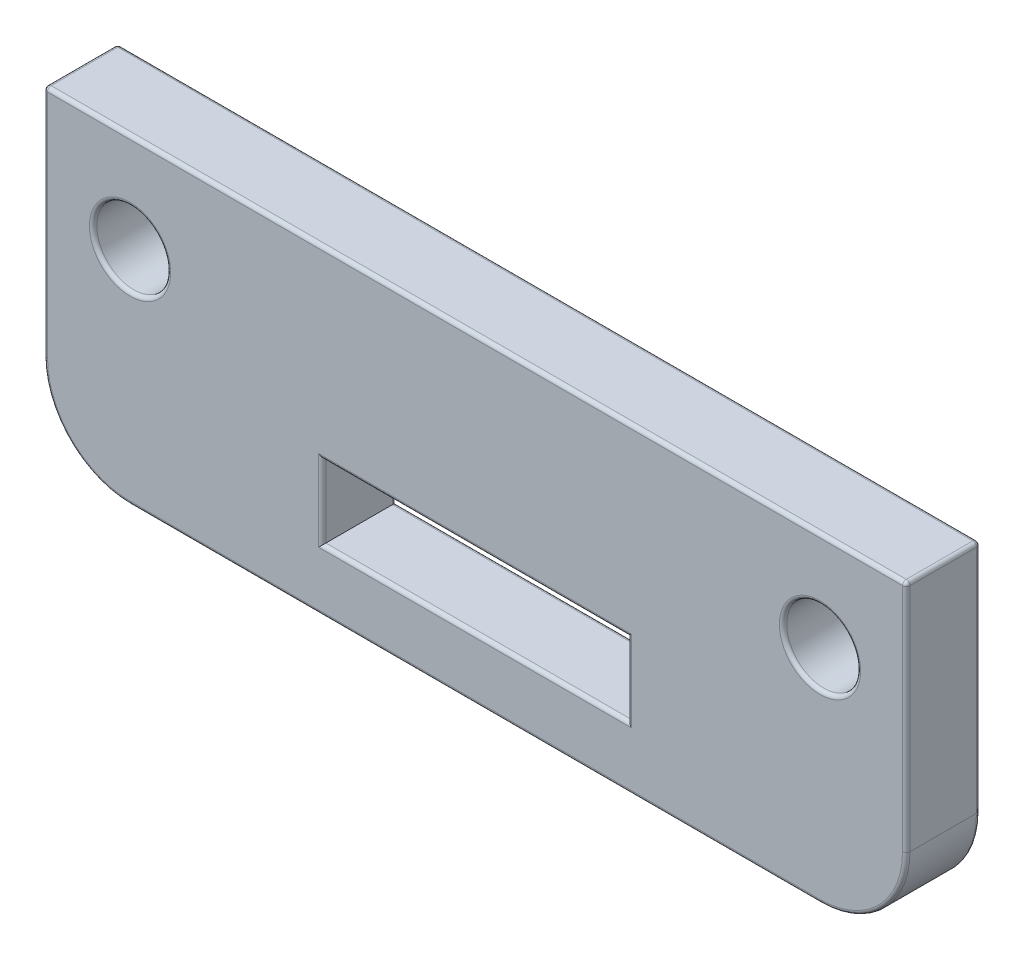
SolidWorks part; units mm, degrees
material "Balsa"
ref_plane "Front Plane" through (0, 0, 0) normal (0, 0, 1) x (1, 0, 0)
ref_plane "Top Plane" through (0, 0, 0) normal (0, 1, 0) x (1, 0, 0)
ref_plane "Right Plane" through (0, 0, 0) normal (1, 0, 0) x (0, 0, -1)
sketch "Sketch1" plane through (0, 0, 0) normal (0, 0, 1) x (1, 0, 0)
  line L0 (0, -19) -> (0, 26) construction
  line L1 (11.5, -6) -> (-11.5, -6)
  line L2 (11.5, -6) -> (11.5, 6)
  line L3 (11.5, 6) -> (-11.5, 6)
  line L4 (-11.5, -6) -> (-11.5, 6)
  line L5 (11.5, -6) -> (-11.5, 6) construction
  line L6 (11.5, 6) -> (-11.5, -6) construction
  line L7 (-6.2, -15) -> (6.2, -15) construction
  line L8 (-6.2, -13.5) -> (6.2, -13.5)
  line L9 (-6.2, -16.5) -> (6.2, -16.5)
  line L10 (-6.2, -13.5) -> (-6.2, -16.5)
  line L11 (-17.5, 9) -> (17.5, 9) construction
  line L12 (-17.5, 9) -> (-17.5, -19)
  line L13 (-17.5, -19) -> (17.5, -19)
  line L14 (17.5, 9) -> (17.5, -19)
  line L15 (6.2, -13.5) -> (6.2, -16.5)
  circle A0 centre (-14, 0) radius 1
  circle A1 centre (-14, -10) radius 1.5
  circle A4 centre (-8.5, 16) radius 2
  circle A5 centre (14, -10) radius 1.5
  circle A6 centre (14, 0) radius 1
  circle A7 centre (8.5, 16) radius 2
  arc A8 (-17.5, 9) -> (17.5, 9) centre (0, 8.4926) cw
  point P0 (0, 0)
  point P10 (-11.5, 0)
  point P11 (0, -15)
  point P33 (0, 26)
  dimension "D5" = 2
  dimension "D7" = 3
  dimension "D12" = 10
  dimension "D13" = 4
  dimension "D1" = 23
  dimension "D2" = 12
  dimension "D3" = 45
  dimension "D4" = 13
  dimension "D6" = 2.5
  dimension "D8" = 10
  dimension "D10" = 12.4
  dimension "D11" = 4
  dimension "D14" = 8.5
  dimension "D15" = 28
  dimension "D16" = 35
  dimension "D17" = 13
extrude "Boss-Extrude1" add sketch "Sketch1" along normal blind 3
fillet "Fillet1" radius 3.5 2 edges at (17.5, -19, 1.5) (-17.5, -19, 1.5)
sketch "Sketch2" plane through (0, 0, 3) normal (0, 0, 1) x (1, 0, 0)
  line L0 (-22.5, -6) -> (27.5, -6)
  line L3 (-11.5, -6) -> (11.5, -6) construction
  line L4 (-17.5, 9) -> (-17.5, -15.5) construction
  dimension "D1" = 50
  dimension "D2" = 5
extrude "Cut-Extrude1" cut sketch "Sketch2" against normal through all both and the other way through all
fillet "Fillet3" radius 0.15 26 edges at (-16.4749, -17.9749, 0) (0, -19, 0) (16.4749, -17.9749, 0) (17.5, -10.75, 0) (0, -6, 0) (-17.5, -10.75, 0) (-12.5, -10, 0) (0, -16.5, 0) (0, -13.5, 0) (12.5, -10, 0) (17.5, -10.75, 3) (16.4749, -17.9749, 3) (0, -19, 3) (-16.4749, -17.9749, 3) (-17.5, -10.75, 3) (0, -6, 3) (-12.5, -10, 3) (0, -16.5, 3) (0, -13.5, 3) (12.5, -10, 3) (17.5, -6, 1.5) (-17.5, -6, 1.5) (6.2, -15, 0) (-6.2, -15, 0) (6.2, -15, 3) (-6.2, -15, 3)
